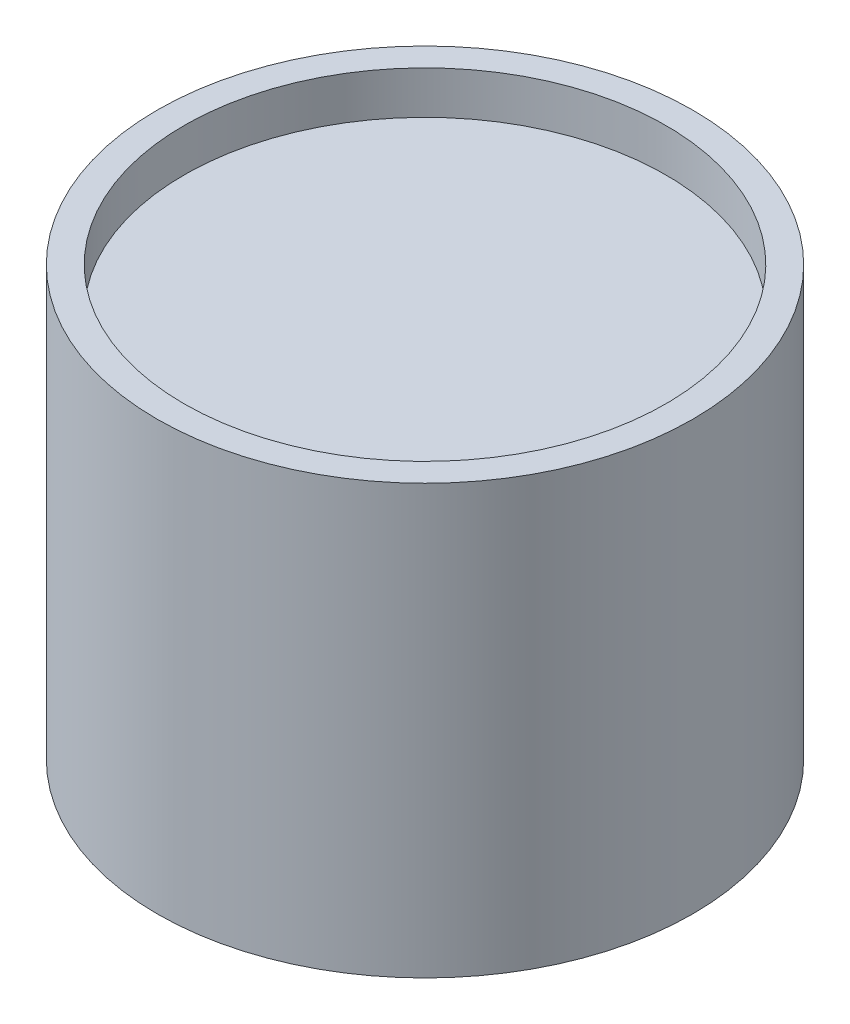
SolidWorks part; units mm, degrees
material "Gomma naturale"
ref_plane "Front Plane" through (0, 0, 0) normal (0, 0, 1) x (1, 0, 0)
ref_plane "Top Plane" through (0, 0, 0) normal (0, 1, 0) x (1, 0, 0)
ref_plane "Right Plane" through (0, 0, 0) normal (1, 0, 0) x (0, 0, -1)
sketch "Schizzo1" plane through (0, 0, 0) normal (0, 1, 0) x (1, 0, 0)
  circle A0 centre (0, 0) radius 5
  dimension "D1" = 10
extrude "Estrusione-Estrusione1" add sketch "Schizzo1" along normal blind 8
sketch "Schizzo2" plane through (0, 8, 0) normal (0, 1, 0) x (1, 0, 0)
  circle A0 centre (0, 0) radius 4.5
  dimension "D1" = 9
extrude "Taglio-Estrusione1" cut sketch "Schizzo2" along direction (0, 1, 0) on the side against the normal blind 0.8
sketch "Schizzo3" plane through (0, 0, 0) normal (0, -1, 0) x (1, 0, 0)
  circle A0 centre (0, 0) radius 4.5
  dimension "D1" = 9
extrude "Taglio-Estrusione2" cut sketch "Schizzo3" along direction (0, 1, 0) on the side against the normal blind 0.8
equation "\"H\"=8"
equation "\"D1@Estrusione-Estrusione1\"=\"H\""
equation "\"D\"=10"
equation "\"D1@Schizzo1\"=\"D\""
equation "\"D1@Schizzo2\"=\"D\"-0.1*\"D\""
equation "\"D1@Taglio-Estrusione1\"=\"H\"*0.1"
equation "\"D1@Schizzo3\"=\"D\"-0.1*\"D\""
equation "\"D1@Taglio-Estrusione2\"=\"H\"*0.1"
